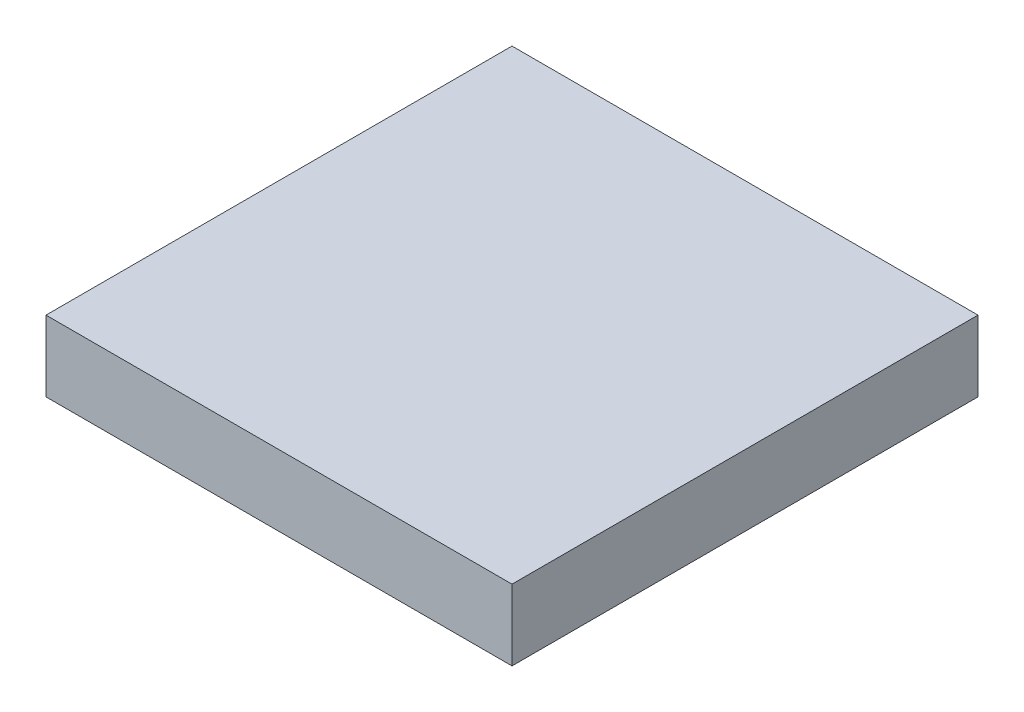
SolidWorks part; units mm, degrees
ref_plane "Front Plane" through (0, 0, 0) normal (0, 0, 1) x (1, 0, 0)
ref_plane "Top Plane" through (0, 0, 0) normal (0, 1, 0) x (1, 0, 0)
ref_plane "Right Plane" through (0, 0, 0) normal (1, 0, 0) x (0, 0, -1)
sketch "Sketch1" plane through (0, 0, 0) normal (0, 1, 0) x (1, 0, 0)
  line L1 (-5, 5) -> (5, 5)
  line L2 (-5, 5) -> (-5, -5)
  line L3 (-5, -5) -> (5, -5)
  line L4 (5, 5) -> (5, -5)
  line L5 (-5, 5) -> (5, -5) construction
  line L6 (-5, -5) -> (5, 5) construction
  point P0 (0, 0)
  dimension "D1" = 10
extrude "Boss-Extrude1" add sketch "Sketch1" along normal blind 1.52
